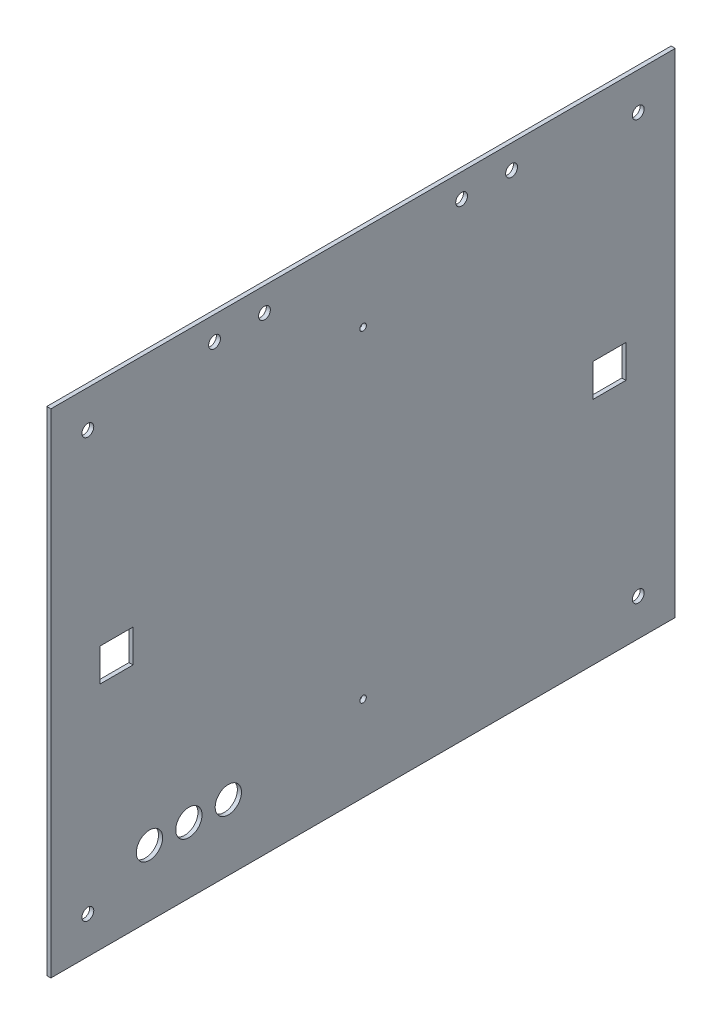
SolidWorks part; units mm, degrees
ref_plane "Front Plane" through (0, 0, 0) normal (0, 0, 1) x (1, 0, 0)
ref_plane "Top Plane" through (0, 0, 0) normal (0, 1, 0) x (1, 0, 0)
ref_plane "Right Plane" through (0, 0, 0) normal (1, 0, 0) x (0, 0, -1)
sketch "Sketch1" plane through (0, 0, 0) normal (1, 0, 0) x (0, 0, -1)
  line L1 (0, 0) -> (241.3, 0)
  line L2 (0, 0) -> (0, 190.5)
  line L3 (0, 190.5) -> (241.3, 190.5)
  line L4 (241.3, 0) -> (241.3, 190.5)
  dimension "D1" = 241.3
  dimension "D2" = 190.5
extrude "Main Body" add sketch "Sketch1" along normal blind 1.5875
sketch "Sketch2" plane through (1.5875, 0, 0) normal (1, 0, 0) x (0, 0, -1)
  line L2 (-1000, 95.25) -> (49000, 95.25) construction
  line L3 (0, 190.5) -> (0, 0) construction
  line L4 (120.65, -809.5) -> (120.65, 49190.5) construction
  line L5 (241.3, 190.5) -> (0, 190.5) construction
  line L6 (1228.6, 95.25) -> (-48771.4, 95.25) construction
  line L7 (241.3, 0) -> (241.3, 190.5) construction
  line L8 (0, 0) -> (241.3, 0) construction
  circle A8 centre (227.0125, 14.2875) radius 2.286
  circle A9 centre (227.0125, 176.2125) radius 2.286
  circle A10 centre (14.2875, 14.2875) radius 2.286
  circle A11 centre (14.2875, 176.2125) radius 2.286
  point P15 (0, 95.25)
  point P20 (120.65, 190.5)
  dimension "D1" = 4.572
  dimension "D3" = 14.2875
  dimension "D2" = 14.2875
extrude "Bolt Holes" cut sketch "Sketch2" against normal through all
sketch "Sketch3" plane through (1.5875, 0, 0) normal (1, 0, 0) x (0, 0, -1)
  line L0 (241.3, 190.5) -> (0, 190.5) construction
  circle A0 centre (63.246, 181.2925) radius 2.286
  circle A1 centre (82.55, 181.2925) radius 2.286
  circle A2 centre (158.75, 181.2925) radius 2.286
  circle A3 centre (178.054, 181.2925) radius 2.286
  point P11 (120.65, 190.5)
  dimension "D1" = 4.572
  dimension "D2" = 19.304
  dimension "D4" = 9.2075
  dimension "D3" = 19.304
  dimension "D5" = 38.1
  dimension "D6" = 38.1
extrude "Locking Mechanism Holes" cut sketch "Sketch3" against normal through all
sketch "Sketch4" plane through (1.5875, 0, 0) normal (1, 0, 0) x (0, 0, -1)
  line L0 (0, 190.5) -> (0, 0) construction
  line L1 (19.05, 101.6) -> (31.75, 101.6)
  line L2 (19.05, 101.6) -> (19.05, 88.9)
  line L3 (19.05, 88.9) -> (31.75, 88.9)
  line L4 (31.75, 101.6) -> (31.75, 88.9)
  line L5 (209.55, 88.9) -> (222.25, 88.9)
  line L6 (209.55, 88.9) -> (209.55, 101.6)
  line L7 (209.55, 101.6) -> (222.25, 101.6)
  line L8 (222.25, 88.9) -> (222.25, 101.6)
  line L9 (241.3, 0) -> (241.3, 190.5) construction
  point P8 (19.05, 95.25)
  point P11 (0, 95.25)
  point P12 (209.55, 95.25)
  dimension "D1" = 12.7
  dimension "D2" = 12.7
  dimension "D3" = 19.05
  dimension "D4" = 19.05
extrude "LED Holes" cut sketch "Sketch4" against normal through all
sketch "Sketch5" plane through (1.5875, 0, 0) normal (1, 0, 0) x (0, 0, -1)
  line L0 (241.3, 190.5) -> (0, 190.5) construction
  line L1 (120.65, 33.02) -> (120.65, 157.48) construction
  line L2 (241.3, 0) -> (241.3, 190.5) construction
  circle A0 centre (120.65, 157.48) radius 1.27
  circle A1 centre (120.65, 33.02) radius 1.27
  point P4 (120.65, 95.25)
  point P7 (120.65, 190.5)
  point P10 (241.3, 95.25)
  dimension "D2" = 2.54
  dimension "D1" = 124.46
extrude "Logo Mount Holes" cut sketch "Sketch5" against normal through all
sketch "Sketch6" plane through (1.5875, 0, 0) normal (1, 0, 0) x (0, 0, -1)
  line L0 (0, 0) -> (241.3, 0) construction
  line L1 (0, 190.5) -> (0, 0) construction
  circle A0 centre (38.1, 25.4) radius 5.08
  circle A1 centre (53.34, 25.4) radius 5.08
  circle A2 centre (68.58, 25.4) radius 5.08
  dimension "D1" = 10.16
  dimension "D3" = 15.24
  dimension "D4" = 25.4
  dimension "D5" = 38.1
  dimension "D2" = 3
extrude "Panel Mount LED Hole" cut sketch "Sketch6" against normal through all
